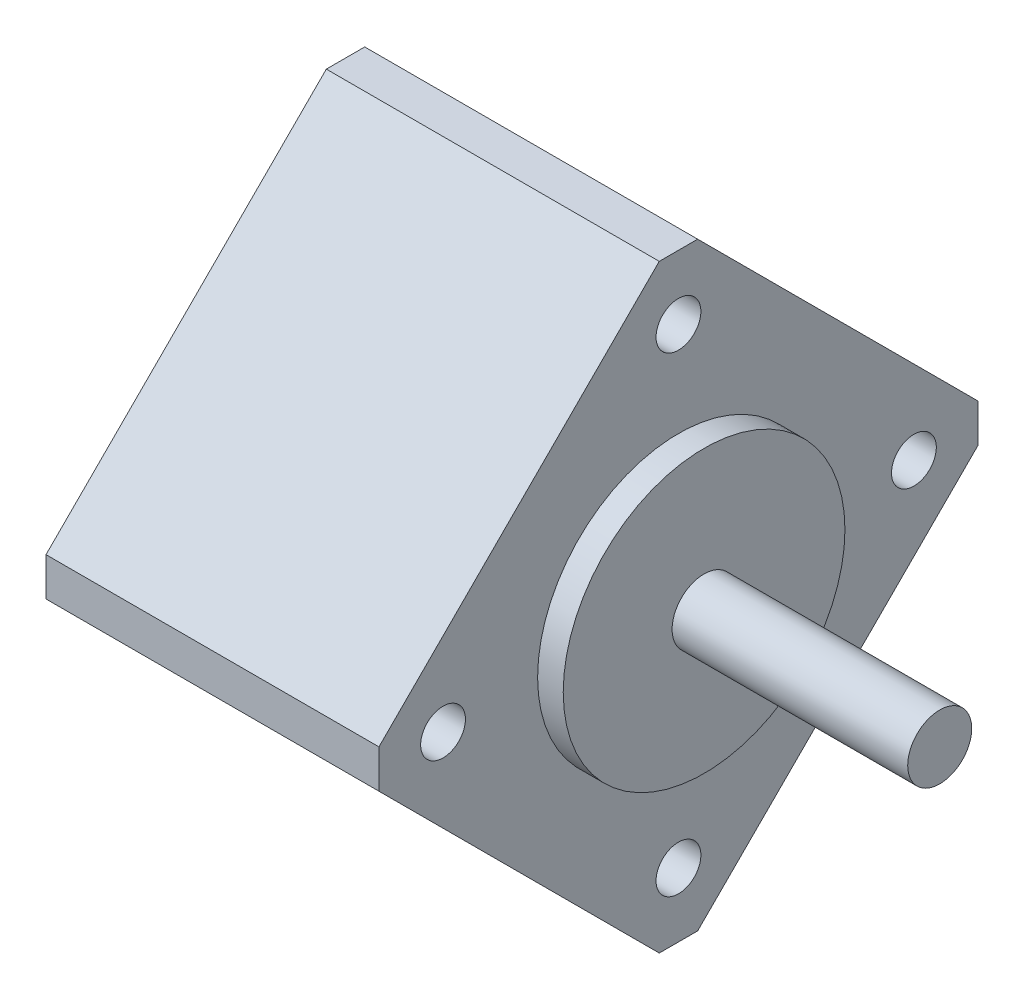
SolidWorks part; units mm, degrees
ref_plane "Front Plane" through (0, 0, 0) normal (0, 0, 1) x (1, 0, 0)
ref_plane "Top Plane" through (0, 0, 0) normal (0, 1, 0) x (1, 0, 0)
ref_plane "Right Plane" through (0, 0, 0) normal (1, 0, 0) x (0, 0, -1)
sketch "Sketch1" plane through (0, 0, 0) normal (0, 0, 1) x (1, 0, 0)
  line L0 (0, 0) -> (58.591, 0) construction
  line L2 (0, 0) -> (18.4, 0)
  line L3 (0, 0) -> (0, 2.5)
  line L4 (0, 2.5) -> (18.4, 2.5)
  line L5 (18.4, 0) -> (18.4, 2.5)
  line L6 (6.0094, 2.5) -> (6.0094, 6)
  line L11 (6.0094, 6) -> (9.9794, 6)
  line L16 (12.9794, 6) -> (12.9794, 3)
  line L17 (12.9794, 3) -> (13.6398, 3)
  line L18 (13.6398, 3) -> (13.6398, 2.5)
  line L19 (13.6398, 2.5) -> (6.0094, 2.5)
  line L22 (13.6398, 2.5) -> (16.1198, 2.5)
  line L23 (13.6398, 2.5) -> (13.6398, 4)
  line L24 (13.6398, 4) -> (16.1198, 4)
  line L25 (16.1198, 2.5) -> (16.1198, 4)
  line L27 (6.0094, 6) -> (9.9794, 6)
  line L28 (6.0094, 6) -> (6.0094, 9)
  line L29 (6.0094, 9) -> (9.9794, 9)
  line L30 (9.9794, 6) -> (9.9794, 9)
  line L31 (6.0094, 9) -> (6.0094, 8.25)
  line L32 (6.0094, 8.25) -> (5.0094, 8.25)
  line L33 (8.6609, 22.001) -> (8.6609, 12.476) construction
  line L34 (5.0094, 12.476) -> (12.3124, 12.476)
  line L35 (9.9794, 9) -> (12.3124, 9)
  line L36 (5.0094, 7.9375) -> (1.7709, 7.9375)
  line L37 (5.0094, 8.25) -> (5.0094, 12.476)
  line L38 (5.0094, 7.9375) -> (5.0094, 13.9365)
  line L39 (5.0094, 13.9365) -> (1.7709, 13.9365)
  line L40 (1.7709, 7.9375) -> (1.7709, 13.9365)
  line L41 (5.0094, 22.001) -> (12.3124, 22.001)
  line L42 (5.0094, 22.001) -> (5.0094, 30.1625)
  line L43 (5.0094, 30.1625) -> (12.3124, 30.1625)
  line L44 (12.3124, 22.001) -> (12.3124, 30.1625)
  line L49 (16.6398, 22.001) -> (16.6398, 7.5)
  line L51 (23.0198, 7.5) -> (23.0198, 6.5)
  line L54 (16.1198, 4) -> (13.6398, 4)
  line L56 (18.0398, 7.5) -> (23.0198, 7.5)
  line L57 (13.3124, 22.001) -> (16.6398, 22.001)
  line L58 (16.1198, 3.5) -> (20.0198, 3.5)
  line L59 (29.9098, 14) -> (26.9098, 11)
  line L60 (4.0094, 31.75) -> (18.0398, 31.75)
  line L61 (18.0398, 7.5) -> (23.0198, 7.5)
  line L62 (18.0398, 7.5) -> (18.0398, 12)
  line L63 (18.0398, 12) -> (23.0198, 12)
  line L64 (23.0198, 7.5) -> (23.0198, 12)
  line L65 (18.0398, 31.75) -> (18.0398, 12)
  line L66 (23.0198, 11) -> (26.9098, 11)
  line L67 (34.8098, 23) -> (31.3098, 19.5)
  line L68 (35.8098, 31) -> (38.7998, 33.99)
  line L69 (29.9098, 14) -> (29.9098, 15)
  line L70 (29.9098, 15) -> (22.9398, 15)
  line L71 (22.9398, 15) -> (21.0398, 15)
  line L72 (18.0398, 7.5) -> (16.6398, 7.5)
  line L73 (21.0398, 15) -> (21.0398, 43)
  line L74 (19.6115, 40) -> (9.6516, 40)
  line L75 (9.6516, 40) -> (4.0094, 40)
  line L76 (21.0398, 43) -> (19.6115, 43)
  line L77 (22.9398, 15) -> (29.9098, 15)
  line L78 (22.9398, 15) -> (22.9398, 21)
  line L79 (22.9398, 21) -> (29.9098, 21)
  line L80 (29.9098, 15) -> (29.9098, 21)
  line L81 (9.6516, 40) -> (19.6115, 40)
  line L82 (9.6516, 40) -> (9.6516, 50)
  line L83 (9.6516, 50) -> (19.6115, 50)
  line L84 (19.6115, 40) -> (19.6115, 50)
  line L85 (4.0094, 40) -> (4.0094, 31.75)
  line L86 (12.9794, 3) -> (12.9794, 2.5)
  line L87 (31.3098, 19.5) -> (29.9098, 19.5)
  line L88 (21.4694, 63.5) -> (21.4694, 51.308)
  line L89 (21.4694, 63.5) -> (25.9398, 63.5)
  line L90 (25.9398, 63.5) -> (25.9398, 25)
  line L91 (27.8398, 25) -> (25.9398, 25)
  line L92 (9.6516, 48) -> (8.2233, 48)
  line L93 (8.2233, 48) -> (8.2233, 53.476)
  line L94 (8.2233, 53.476) -> (19.6115, 53.476)
  line L95 (19.6115, 53.476) -> (19.6115, 50)
  line L96 (13.9174, 63.001) -> (13.9174, 53.476) construction
  line L97 (8.2233, 63.001) -> (19.6115, 63.001)
  line L98 (8.2233, 63.001) -> (8.2233, 68.2625)
  line L99 (8.2233, 68.2625) -> (19.6115, 68.2625)
  line L100 (19.6115, 63.001) -> (19.6115, 68.2625)
  line L101 (12.9794, 6) -> (11.9794, 6)
  line L102 (8.2233, 44.825) -> (4.9848, 44.825)
  line L103 (8.2233, 44.825) -> (8.2233, 54.9365)
  line L104 (8.2233, 54.9365) -> (4.9848, 54.9365)
  line L106 (9.9794, 6) -> (10.8794, 6)
  line L107 (27.8398, 25) -> (34.8098, 25)
  line L108 (34.8098, 25) -> (34.8098, 23)
  line L109 (0, 0) -> (-2, 0)
  line L110 (0, 0) -> (0, 11)
  line L111 (27.8398, 25) -> (34.8098, 25)
  line L112 (27.8398, 25) -> (27.8398, 32.5)
  line L113 (27.8398, 32.5) -> (34.8098, 32.5)
  line L114 (34.8098, 25) -> (34.8098, 32.5)
  line L115 (35.8098, 31) -> (34.8098, 31)
  line L116 (27.8398, 32.5) -> (27.8398, 64.5)
  line L117 (20.5849, 74.025) -> (6.2499, 74.025)
  line L118 (6.2499, 74.025) -> (6.2499, 76.2)
  line L119 (38.7998, 47.29) -> (30.8398, 55.25)
  line L120 (0, 11) -> (-2, 11)
  line L121 (38.7998, 43.815) -> (30.8623, 43.815)
  line L123 (-4.8152, 69.85) -> (1.5348, 76.2)
  line L124 (38.7998, 47.29) -> (38.7998, 33.99)
  line L125 (-2, 0) -> (-2, 11)
  line L126 (38.7998, 37.465) -> (30.8623, 37.465)
  line L127 (30.8623, 43.815) -> (30.8623, 37.465)
  line L128 (6.0094, 2.5) -> (6.0094, 0)
  line L129 (-0.0152, 63.5) -> (-0.0152, 30)
  line L132 (4.9848, 63.5) -> (-0.0152, 63.5)
  line L136 (-1.8152, 30) -> (-11.7752, 30)
  line L138 (-13.7752, 25.4) -> (-2, 25.4)
  line L139 (-2, 25.4) -> (-2, 11.5)
  line L140 (27.8398, 64.5) -> (20.5849, 64.5)
  line L141 (-1.8152, 30) -> (-11.7752, 30)
  line L142 (-1.8152, 30) -> (-1.8152, 39)
  line L143 (-1.8152, 39) -> (-11.7752, 39)
  line L144 (-11.7752, 30) -> (-11.7752, 39)
  line L145 (20.5849, 64.5) -> (20.5849, 74.025)
  line L146 (-12.7752, 37) -> (-12.7752, 47.29)
  line L147 (-12.7752, 37) -> (-11.7752, 37)
  line L148 (30.8398, 55.25) -> (30.8398, 76.2)
  line L149 (11.9794, 6) -> (11.9794, 5.45)
  line L154 (-2, 11.5) -> (0.5, 11.5)
  line L155 (4.9848, 60.6197) -> (24.0348, 60.6197)
  line L160 (4.9848, 60.6197) -> (4.9848, 55.8572)
  line L161 (4.9848, 55.8572) -> (24.0348, 55.8572)
  line L166 (24.0348, 60.6197) -> (24.0348, 55.8572)
  line L167 (4.9848, 60.6197) -> (24.0348, 55.8572) construction
  line L172 (4.9848, 55.8572) -> (24.0348, 60.6197) construction
  line L173 (24.0348, 62.2072) -> (25.9398, 62.2072)
  line L174 (11.9794, 5.45) -> (10.8794, 5.45)
  line L175 (10.8794, 6) -> (10.8794, 5.45)
  line L176 (24.0348, 62.2072) -> (24.0348, 54.2697)
  line L177 (24.0348, 54.2697) -> (25.9398, 54.2697)
  line L178 (25.9398, 62.2072) -> (25.9398, 54.2697)
  line L179 (24.0348, 62.2072) -> (25.9398, 54.2697) construction
  line L180 (24.0348, 54.2697) -> (25.9398, 62.2072) construction
  line L181 (3, 19.6197) -> (15.7, 19.6197)
  line L182 (3, 19.6197) -> (3, 14.8572)
  line L183 (3, 14.8572) -> (15.7, 14.8572)
  line L184 (15.7, 19.6197) -> (15.7, 14.8572)
  line L185 (3, 19.6197) -> (15.7, 14.8572) construction
  line L186 (3, 14.8572) -> (15.7, 19.6197) construction
  line L187 (15.7, 21.2072) -> (16.6398, 21.2072)
  line L188 (15.7, 21.2072) -> (15.7, 13.2697)
  line L189 (15.7, 13.2697) -> (16.6398, 13.2697)
  line L190 (16.6398, 21.2072) -> (16.6398, 13.2697)
  line L191 (15.7, 21.2072) -> (16.6398, 13.2697) construction
  line L192 (15.7, 13.2697) -> (16.6398, 21.2072) construction
  line L193 (0.5, 11.5) -> (0.5, 6.9375)
  line L194 (0.5, 6.9375) -> (1.7709, 6.9375)
  line L195 (23.0198, 6.5) -> (20.0198, 3.5)
  line L196 (4.9848, 63.5) -> (4.9848, 54.9365)
  line L197 (3, 43.825) -> (4.9848, 43.825)
  line L198 (1.7709, 6.9375) -> (1.7709, 7.9375)
  line L199 (6.0094, 0) -> (12.9794, 0)
  line L200 (12.9794, 0) -> (12.9794, 2.5)
  line L201 (18.0398, 31.75) -> (18.0398, 35.875)
  line L202 (18.0398, 35.875) -> (21.0398, 35.875)
  line L203 (30.8398, 76.2) -> (6.2499, 76.2)
  line L204 (2.8049, 69.85) -> (7.2499, 69.85) construction
  line L205 (7.2499, 67.4688) -> (26.2999, 67.4688)
  line L206 (7.2499, 74.025) -> (7.2499, 64.5)
  line L207 (7.2499, 64.5) -> (-1.8152, 64.5)
  line L208 (-1.8152, 64.5) -> (-1.8152, 39)
  line L209 (-12.7752, 47.29) -> (-4.8152, 55.25)
  line L210 (-4.8152, 55.25) -> (-4.8152, 69.85)
  line L211 (7.2499, 67.4688) -> (7.2499, 72.2312)
  line L212 (7.2499, 72.2312) -> (26.2999, 72.2313)
  line L213 (26.2999, 67.4688) -> (26.2999, 72.2313)
  line L214 (26.2999, 73.8187) -> (30.8398, 73.8187)
  line L215 (26.2999, 73.8187) -> (26.2999, 65.8813)
  line L216 (26.2999, 65.8813) -> (30.8398, 65.8813)
  line L217 (30.8398, 73.8187) -> (30.8398, 65.8813)
  line L218 (2.8049, 72.2313) -> (25.0299, 72.2313)
  line L219 (2.8049, 72.2313) -> (2.8049, 67.4687)
  line L220 (2.8049, 67.4687) -> (25.0299, 67.4687)
  line L221 (25.0299, 72.2313) -> (25.0299, 67.4687)
  line L222 (25.0299, 69.85) -> (20.5849, 69.85) construction
  line L223 (21.4694, 51.308) -> (22.9398, 51.308)
  line L224 (22.9398, 51.308) -> (22.9398, 21)
  line L225 (13.6398, 4) -> (13.6398, 12.2697)
  line L226 (13.6398, 12.2697) -> (13.3124, 12.2697)
  line L227 (13.3124, 12.2697) -> (13.3124, 22.001)
  line L228 (12.3124, 9) -> (12.3124, 12.476)
  line L229 (-1.8152, 30) -> (-0.0152, 30)
  line L230 (8.2233, 65.6317) -> (2.8049, 65.6317) construction
  line L231 (19.6115, 65.6317) -> (25.0299, 65.6317) construction
  line L232 (1.5348, 76.2) -> (6.2499, 76.2)
  line L233 (-11.7752, 30) -> (-13.7752, 30)
  line L234 (-13.7752, 30) -> (-13.7752, 25.4)
  line L235 (3, 13.9365) -> (3, 43.825)
  line L236 (4.9848, 54.9365) -> (4.9848, 44.825)
  line L237 (4.9848, 43.825) -> (4.9848, 44.825)
  circle A0 centre (26.8898, 25.95) radius 0.95
  circle A1 centre (21.9898, 15.95) radius 0.95
  circle A2 centre (17.3398, 8.2) radius 0.7
  circle A3 centre (10.4294, 6.45) radius 0.45
  circle A4 centre (-0.9152, 30.9) radius 0.9
  point P7 (24.9873, 58.2385)
  point P131 (16.1699, 17.2385)
  point P135 (14.5098, 58.2385)
  point P146 (9.35, 17.2385)
sketch "Sketch2" plane through (0, 0, 0) normal (0, 0, 1) x (1, 0, 0)
  line L0 (0, 0) -> (-2, 0) construction
  line L1 (0, 11) -> (-2, 11) construction
  line L2 (-2, 0) -> (-2, 11) construction
  line L3 (0, 0) -> (0, 11) construction
  line L4 (18.4, 0) -> (18.4, 2.5) construction
  line L5 (0, 0) -> (18.4, 0) construction
  line L6 (0, 2.5) -> (18.4, 2.5) construction
  line L7 (0, 0) -> (-2, 0)
  line L8 (0, 11) -> (-2, 11)
  line L9 (-2, 0) -> (-2, 11)
  line L10 (0, 0) -> (0, 11)
  line L11 (18.4, 0) -> (18.4, 2.5)
  line L12 (0, 0) -> (18.4, 0)
  line L13 (0, 2.5) -> (18.4, 2.5)
revolve "Revolve1" add sketch "Sketch2" angle 360 about L0
sketch "Sketch3" plane through (-2, 0, 0) normal (-1, 0, 0) x (0, 0, 1)
  line L0 (0, 23.3902) -> (1.5, 23.3902)
  line L1 (1.5, 23.3902) -> (23.3902, 1.5)
  line L2 (23.3902, 1.5) -> (23.3902, 0)
  line L3 (23.3902, -1.5) -> (1.5, -23.3902)
  line L4 (1.5, -23.3902) -> (0, -23.3902)
  line L5 (23.3902, 0) -> (23.3902, -1.5)
  line L6 (-1.5, -23.3902) -> (-23.3902, -1.5)
  line L7 (-23.3902, -1.5) -> (-23.3902, 0)
  line L8 (0, -23.3902) -> (-1.5, -23.3902)
  line L9 (-23.3902, 1.5) -> (-1.5, 23.3902)
  line L10 (-1.5, 23.3902) -> (0, 23.3902)
  line L11 (-23.3902, 0) -> (-23.3902, 1.5)
  circle A0 centre (0, 18.3848) radius 1.75
  circle A1 centre (18.3848, 0) radius 1.75
  circle A2 centre (0, -18.3848) radius 1.75
  circle A3 centre (-18.3848, 0) radius 1.75
  point P19 (0, 0)
  point P25 (0, 0)
  dimension "D5" = 3.5
  dimension "D2" = 35.2
  dimension "D3" = 3
  dimension "D6" = 26
  dimension "D1" = 4
  dimension "D4" = 4
extrude "Boss-Extrude1" add sketch "Sketch3" along normal blind 26
